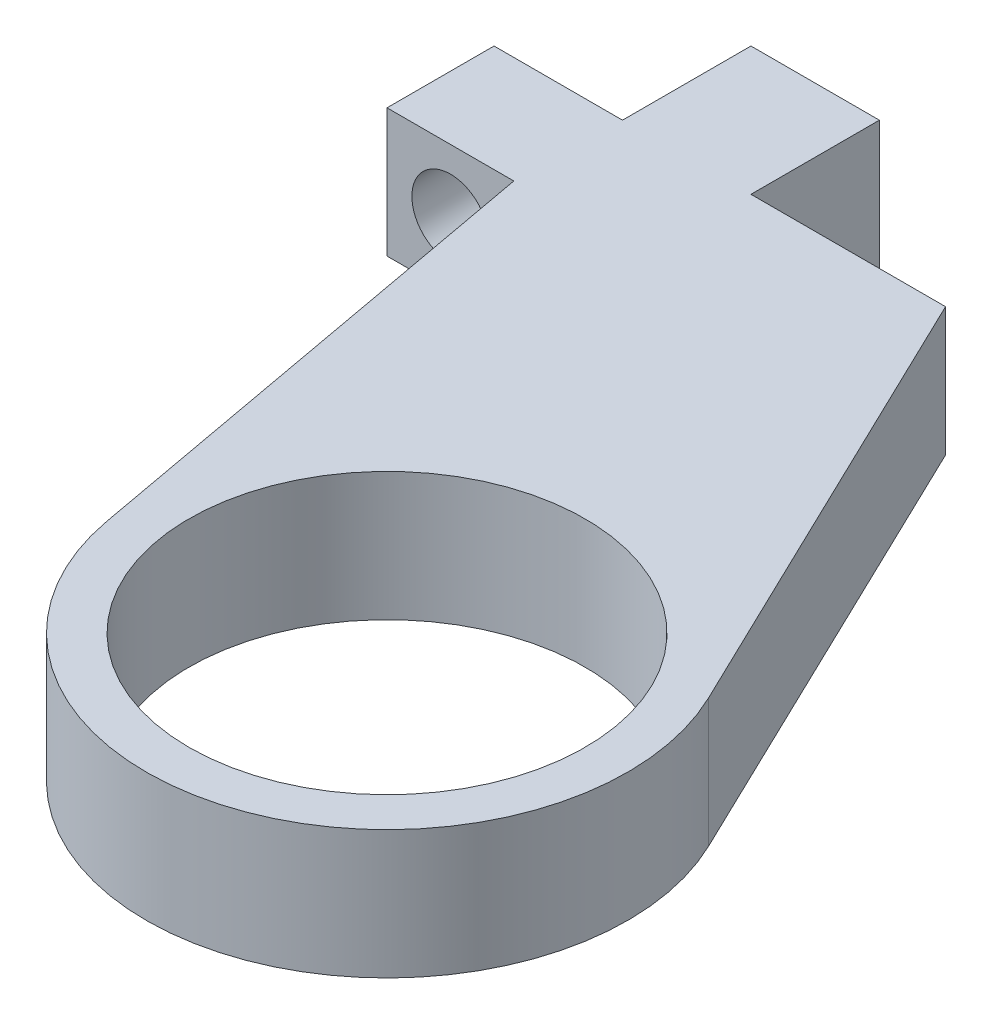
SolidWorks part; units mm, degrees
ref_plane "Front Plane" through (0, 0, 0) normal (0, 0, 1) x (1, 0, 0)
ref_plane "Top Plane" through (0, 0, 0) normal (0, 1, 0) x (1, 0, 0)
ref_plane "Right Plane" through (0, 0, 0) normal (1, 0, 0) x (0, 0, -1)
sketch "Sketch1" plane through (0, 0, 0) normal (0, 1, 0) x (1, 0, 0)
  line L0 (-21.25, 32.25) -> (-21.25, -14.7371) construction
  line L1 (-21.25, 32.25) -> (18.262, 32.25) construction
  line L2 (-21.25, 26.25) -> (-15.25, 26.25)
  line L3 (-15.25, 26.25) -> (-15.25, 32.25)
  line L4 (-15.25, 32.25) -> (-9.25, 32.25)
  line L5 (-9.25, 32.25) -> (-9.25, 26.25)
  line L6 (-21.25, 26.25) -> (-21.25, 21.25)
  line L7 (-21.25, 21.25) -> (-15.3276, 21.25)
  line L8 (-9.25, 26.25) -> (-9.25, -14.7371) construction
  line L9 (-15.3276, 21.25) -> (-11.0661, -2.026)
  line L10 (-9.25, 26.25) -> (-0.1587, 26.25)
  line L11 (-0.1587, 26.25) -> (10.1352, 4.8827)
  circle A0 centre (0, 0) radius 9.25
  arc A1 (-11.0661, -2.026) -> (10.1352, 4.8827) centre (0, 0) ccw
  dimension "D1" = 18.5
  dimension "D2" = 22.5
  dimension "D3" = 32.25
  dimension "D4" = 6
  dimension "D5" = 6
  dimension "D6" = 6
  dimension "D7" = 5
  dimension "D8" = 6
extrude "Boss-Extrude1" add sketch "Sketch1" along normal blind 6
sketch "Sketch2" plane through (0, 0, -21.25) normal (0, 0, 1) x (1, 0, 0)
  line L0 (-18.2888, 6) -> (-18.2888, 0) construction
  line L1 (-21.25, 6) -> (-15.3276, 6) construction
  line L2 (-21.25, 0) -> (-15.3276, 0) construction
  circle A0 centre (-18.2888, 3) radius 1.8
extrude "Cut-Extrude1" cut sketch "Sketch2" against normal through all
